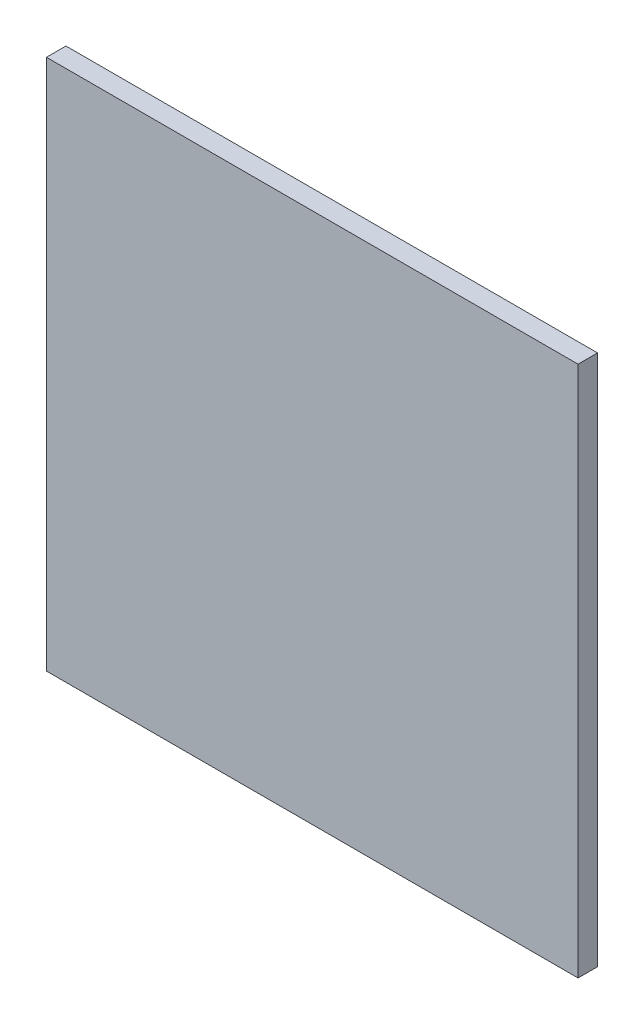
SolidWorks part; units mm, degrees
ref_plane "前视基准面" through (0, 0, 0) normal (0, 0, 1) x (1, 0, 0)
ref_plane "上视基准面" through (0, 0, 0) normal (0, 1, 0) x (1, 0, 0)
ref_plane "右视基准面" through (0, 0, 0) normal (1, 0, 0) x (0, 0, -1)
sketch "草图1" plane through (0, 0, 0) normal (0, 0, 1) x (1, 0, 0)
  line L1 (-15, -15) -> (15, -15)
  line L2 (-15, -15) -> (-15, 15)
  line L3 (-15, 15) -> (15, 15)
  line L4 (15, -15) -> (15, 15)
  line L5 (-15, -15) -> (15, 15) construction
  line L6 (-15, 15) -> (15, -15) construction
  circle A0 centre (0, 0) radius 8.75 construction
  dimension "D1" = 17.5
  dimension "D2" = 30
  dimension "D3" = 30
extrude "凸台-拉伸1" add sketch "草图1" along normal blind 1.1
